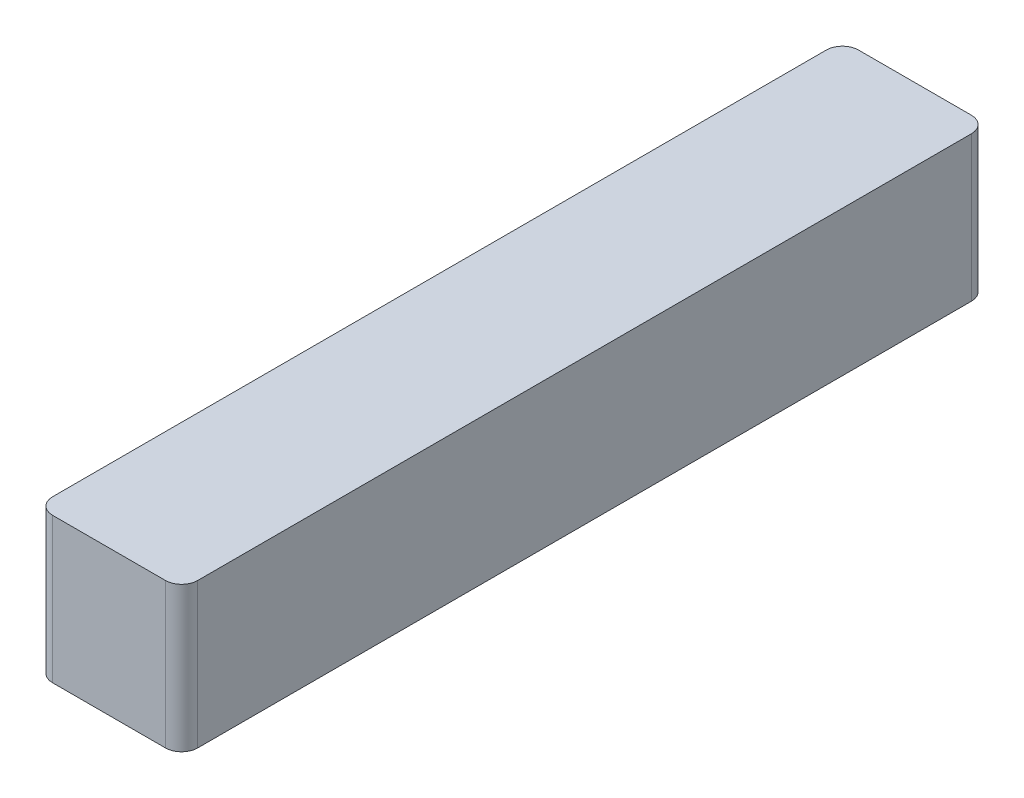
SolidWorks part; units mm, degrees
ref_plane "Front" through (0, 0, 0) normal (0, 0, 1) x (1, 0, 0)
ref_plane "Top" through (0, 0, 0) normal (0, 1, 0) x (1, 0, 0)
ref_plane "Right" through (0, 0, 0) normal (1, 0, 0) x (0, 0, -1)
sketch "Sketch1" plane through (0, 0, 0) normal (0, 0, 1) x (1, 0, 0)
  line L1 (-1.143, 1.143) -> (1.143, 1.143)
  line L2 (-1.143, 1.143) -> (-1.143, -1.143)
  line L3 (-1.143, -1.143) -> (1.143, -1.143)
  line L4 (1.143, 1.143) -> (1.143, -1.143)
  line L5 (-1.143, 1.143) -> (1.143, -1.143) construction
  line L6 (-1.143, -1.143) -> (1.143, 1.143) construction
  point P0 (0, 0)
  dimension "D1" = 2.286
extrude "Boss-Extrude1" add sketch "Sketch1" along normal blind 12.7
fillet "Fillet1" radius 0.254 4 edges at (-1.143, 0, 0) (1.143, 0, 0) (-1.143, 0, 12.7) (1.143, 0, 12.7)
